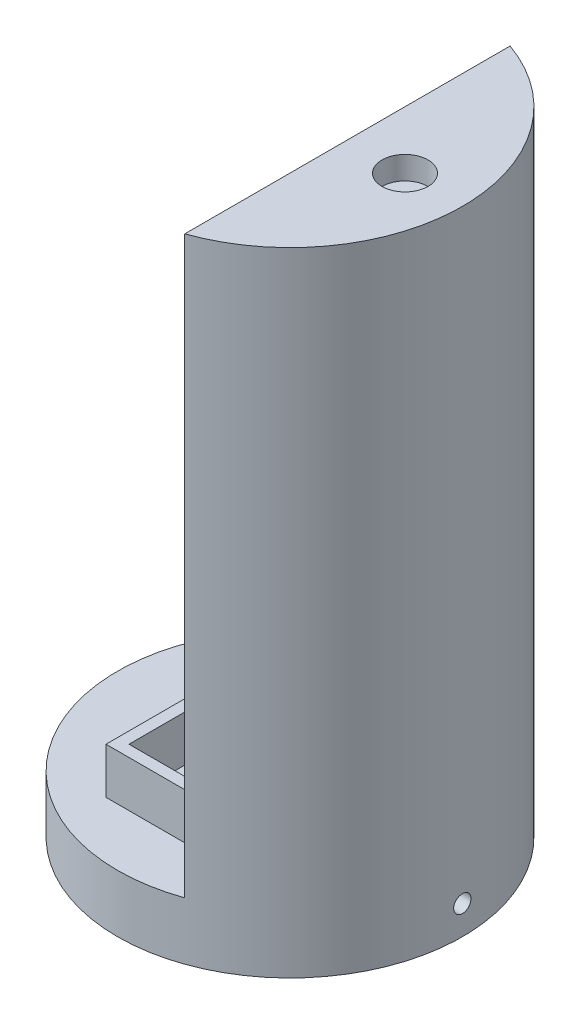
SolidWorks part; units mm, degrees
ref_plane "Front Plane" through (0, 0, 0) normal (0, 0, 1) x (1, 0, 0)
ref_plane "Top Plane" through (0, 0, 0) normal (0, 1, 0) x (1, 0, 0)
ref_plane "Right Plane" through (0, 0, 0) normal (1, 0, 0) x (0, 0, -1)
sketch "Sketch1" plane through (0, 0, 0) normal (0, 1, 0) x (1, 0, 0)
  circle A0 centre (0, 0) radius 38.1
  dimension "D1" = 76.2
extrude "Boss-Extrude1" add sketch "Sketch1" along normal blind 12.7
sketch "Sketch2" plane through (0, 12.7, 0) normal (0, 1, 0) x (1, 0, 0)
  line L1 (-15.24, 25.4) -> (15.24, 25.4)
  line L2 (-15.24, 25.4) -> (-15.24, -25.4)
  line L3 (-15.24, -25.4) -> (15.24, -25.4)
  line L4 (15.24, 25.4) -> (15.24, -25.4)
  dimension "D1" = 25.4
  dimension "D2" = 50.8
  dimension "D3" = 30.48
  dimension "D4" = 15.24
extrude "Boss-Extrude2" add sketch "Sketch2" along normal blind 10.16
sketch "Sketch3" plane through (0, 22.86, 0) normal (0, 1, 0) x (1, 0, 0)
  line L0 (15.24, -25.4) -> (15.24, 25.4) construction
  line L1 (-12.7, 22.86) -> (12.7, 22.86)
  line L2 (-12.7, 22.86) -> (-12.7, -22.86)
  line L3 (-12.7, -22.86) -> (12.7, -22.86)
  line L4 (12.7, 22.86) -> (12.7, -22.86)
  line L5 (-15.24, 25.4) -> (-15.24, -25.4) construction
  line L6 (15.24, 25.4) -> (-15.24, 25.4) construction
  line L7 (-15.24, -25.4) -> (15.24, -25.4) construction
  dimension "D1" = 2.54
  dimension "D2" = 2.54
  dimension "D3" = 2.54
  dimension "D4" = 2.54
extrude "Cut-Extrude1" cut sketch "Sketch3" against normal up to surface (10.16 mm away) up to face at (0, 12.7, 0)
sketch "Sketch4" plane through (0, 12.7, 0) normal (0, 1, 0) x (1, 0, 0)
  line L0 (12.6806, 25.4) -> (12.6806, 35.9279)
  line L1 (15.24, 25.4) -> (-15.24, 25.4) construction
  line L2 (12.6806, 25.4) -> (12.6806, -35.9279)
  circle A0 centre (0, 0) radius 38.1 construction
  arc A1 (12.6806, -35.9279) -> (12.6806, 35.9279) centre (0, 0) ccw
extrude "Boss-Extrude3" add sketch "Sketch4" along normal blind 127
sketch "Sketch5" plane through (12.6806, 0, 0) normal (-1, 0, 0) x (0, 0, 1)
  circle A0 centre (-25.8184, 129.7815) radius 1.27
  circle A1 centre (24.4674, 129.7815) radius 1.27
  circle A2 centre (-25.8184, 40.8771) radius 1.27
  circle A3 centre (24.4674, 40.8771) radius 1.27
  point P8 (-25.8184, 40.8771)
  point P9 (24.4674, 40.8771)
  point P10 (24.4674, 129.7815)
  point P11 (-25.8184, 129.7815)
  dimension "D1" = 2.54
  dimension "D2" = 2.54
  dimension "D3" = 2.54
  dimension "D4" = 2.54
extrude "Cut-Extrude2" cut sketch "Sketch5" against normal blind 5.08
sketch "Sketch6" plane through (0, 139.7, 0) normal (0, 1, 0) x (1, 0, 0)
  circle A0 centre (25.4, 0) radius 5.08
  dimension "D1" = 10.16
  dimension "D2" = 25.4
extrude "Cut-Extrude3" cut sketch "Sketch6" against normal blind 5.08
sketch "Sketch7" plane through (0, 0, 0) normal (1, 0, 0) x (0, 0, -1)
  circle A0 centre (0, 6.35) radius 1.905
  dimension "D1" = 3.81
extrude "Cut-Extrude4" cut sketch "Sketch7" against normal blind 54.61 and the other way blind 57.658
